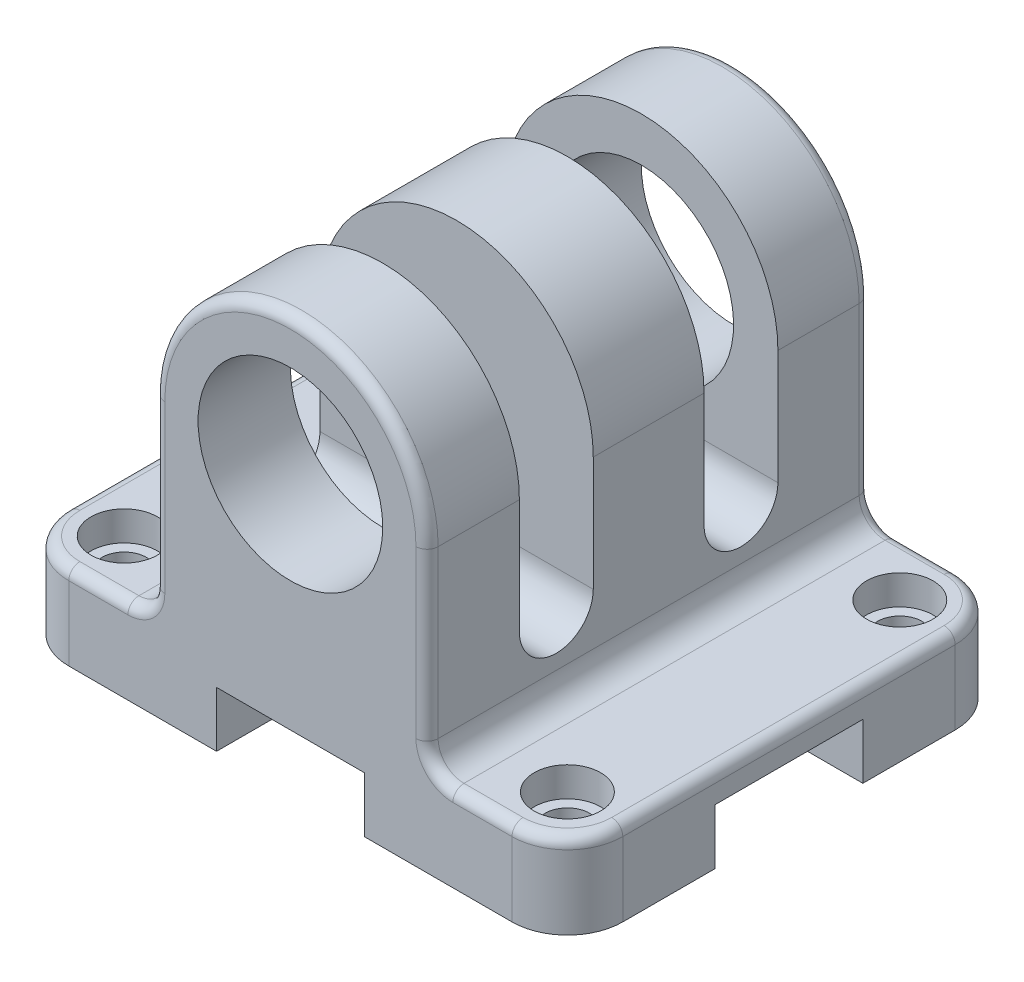
SolidWorks part; units mm, degrees
ref_plane "정면" through (0, 0, 0) normal (0, 0, 1) x (1, 0, 0)
ref_plane "윗면" through (0, 0, 0) normal (0, 1, 0) x (1, 0, 0)
ref_plane "우측면" through (0, 0, 0) normal (1, 0, 0) x (0, 0, -1)
sketch "스케치1" plane through (0, 0, 0) normal (0, 0, 1) x (1, 0, 0)
  line L0 (-75, 0) -> (-20, 0)
  line L1 (75, 0) -> (75, 23)
  line L2 (75, 23) -> (44, 23)
  line L3 (37, 30) -> (37, 75)
  line L5 (-37, 75) -> (-37, 30)
  line L6 (-44, 23) -> (-75, 23)
  line L7 (-75, 23) -> (-75, 0)
  line L8 (0, 207.36) -> (0, -131.4514) construction
  line L9 (20, 0) -> (75, 0)
  line L10 (-20, 15) -> (20, 15)
  line L11 (-20, 15) -> (-20, 0)
  line L13 (20, 15) -> (20, 0)
  arc A0 (37, 75) -> (-37, 75) centre (0, 75) ccw
  arc A3 (-44, 23) -> (-37, 30) centre (-44, 30) ccw
  arc A4 (44, 23) -> (37, 30) centre (44, 30) cw
  point P4 (0, 0)
  point P7 (75, 11.5)
  point P9 (0, 0)
  point P12 (0, 0)
  dimension "D3" = 74
  dimension "D8" = 7
  dimension "D1" = 75
  dimension "D2" = 150
  dimension "D4" = 75
  dimension "D5" = 23
  dimension "D6" = 23
  dimension "D9" = 40
  dimension "D10" = 15
  dimension "D11" = 20
extrude "보스-돌출1" add sketch "스케치1" along normal mid plane 120
ref_plane "평면1" through (0, 0, 35) normal (0, 0, 1) x (1, 0, 0)
ref_plane "평면2" through (0, 0, -15) normal (0, 0, 1) x (1, 0, 0)
sketch "스케치3" plane through (0, 0, 0) normal (1, 0, 0) x (0, 0, -1)
  line L0 (-25, 44) -> (-25, 156) construction
  line L1 (-35, 44) -> (-35, 156)
  line L2 (-15, 44) -> (-15, 156)
  line L3 (-60, 0) -> (60, 0) construction
  line L4 (-35, 61.6) -> (-35, -61.6) construction
  line L5 (0, 192.6317) -> (0, -67.5597) construction
  line L6 (25, 44) -> (25, 156) construction
  line L7 (35, 44) -> (35, 156)
  line L8 (15, 44) -> (15, 156)
  line L9 (-60, 0) -> (60, 0) construction
  line L10 (20, 0) -> (-20, 0)
  line L11 (20, 0) -> (20, 15)
  line L12 (20, 15) -> (-20, 15)
  line L13 (-20, 0) -> (-20, 15)
  arc A0 (-35, 44) -> (-15, 44) centre (-25, 44) ccw
  arc A1 (-15, 156) -> (-35, 156) centre (-25, 156) ccw
  arc A2 (35, 44) -> (15, 44) centre (25, 44) cw
  arc A3 (15, 156) -> (35, 156) centre (25, 156) cw
  point P2 (-25, 100)
  point P13 (25, 100)
  dimension "D1" = 10
  dimension "D2" = 44
  dimension "D3" = 112
  dimension "D4" = 15
  dimension "D5" = 20
  dimension "D6" = 40
extrude "컷-돌출1" cut sketch "스케치3" against normal through all both and the other way through all
sketch "스케치4" plane through (0, 0, 60) normal (0, 0, 1) x (1, 0, 0)
  circle A0 centre (0, 75) radius 25
  arc A1 (37, 75) -> (-37, 75) centre (0, 75) ccw construction
  dimension "D1" = 50
extrude "컷-돌출2" cut sketch "스케치4" against normal up to next (25 mm away)
mirror "대칭 복사1" about plane through (0, 0, 0) normal (0, 0, 1) of "컷-돌출2"
sketch "스케치5" plane through (0, 0, 15) normal (0, 0, 1) x (1, 0, 0)
  circle A0 centre (0, 75) radius 7
  circle A1 centre (0, 75) radius 25 construction
  dimension "D1" = 14
extrude "컷-돌출3" cut sketch "스케치5" against normal up to next
fillet "필렛1" radius 15 4 edges at (-75, 11.5, -60) (75, 11.5, -60) (75, 11.5, 60) (-75, 11.5, 60)
hole_wizard "M2 소켓 머리 캡 나사용 카운터보어1" positions "스케치8" profile "스케치10" counterbore size "M2" standard "KS" end condition through all
sketch "스케치8" plane through (0, 23, 0) normal (0, 1, 0) x (1, 0, 0)
  arc A0 (-60, 60) -> (-75, 45) centre (-60, 45) ccw construction
  arc A1 (-75, -45) -> (-60, -60) centre (-60, -45) ccw construction
  point P0 (-60, 45)
  point P2 (-60, -45)
  point P5 (0, 0)
  point P6 (0, 0)
  point P10 (0, 0)
sketch "스케치10" plane through (-60, 23, -45) normal (1, 0, 0) x (0, 0, 1)
  line L0 (0, 0) -> (0, 23)
  line L1 (0, 23) -> (6, 23)
  line L3 (6, 23) -> (6, 8)
  line L4 (6, 8) -> (9, 8)
  line L5 (9, 8) -> (9, 0)
  line L7 (9, 0) -> (0, 0)
  line L11 (0, -6.35) -> (0, 107.95) construction
  dimension "관통 구멍 지름" = 12
  dimension "관통 구멍 깊이" = 23
  dimension "카운터보어 지름" = 18
  dimension "카운터보어 깊이" = 8
mirror "대칭 복사2" about plane through (0, 0, 0) normal (1, 0, 0) of "M2 소켓 머리 캡 나사용 카운터보어1"
fillet "필렛2" radius 3 20 edges at (39.0503, 25.0503, 60) (52, 23, 60) (70.6066, 23, 55.6066) (75, 23, 0) (70.6066, 23, -55.6066) (52, 23, -60) (39.0503, 25.0503, -60) (37, 52.5, -60) (0, 112, -60) (-37, 52.5, -60) (-39.0503, 25.0503, -60) (-52, 23, -60) (-70.6066, 23, -55.6066) (-75, 23, 0) (-70.6066, 23, 55.6066) (-52, 23, 60) (-39.0503, 25.0503, 60) (-37, 52.5, 60) (0, 112, 60) (37, 52.5, 60)
sketch "스케치11" plane through (0, 0, 0) normal (0, -1, 0) x (1, 0, 0)
  circle A0 centre (0, 0) radius 45
extrude "컷-돌출4" cut sketch "스케치11" against normal up to vertex (15 mm away)
sketch "스케치12" plane through (0, 15, 0) normal (0, -1, 0) x (1, 0, 0)
  circle A0 centre (0, 0) radius 25
extrude "보스-돌출2" add sketch "스케치12" along normal up to vertex (15 mm away)
